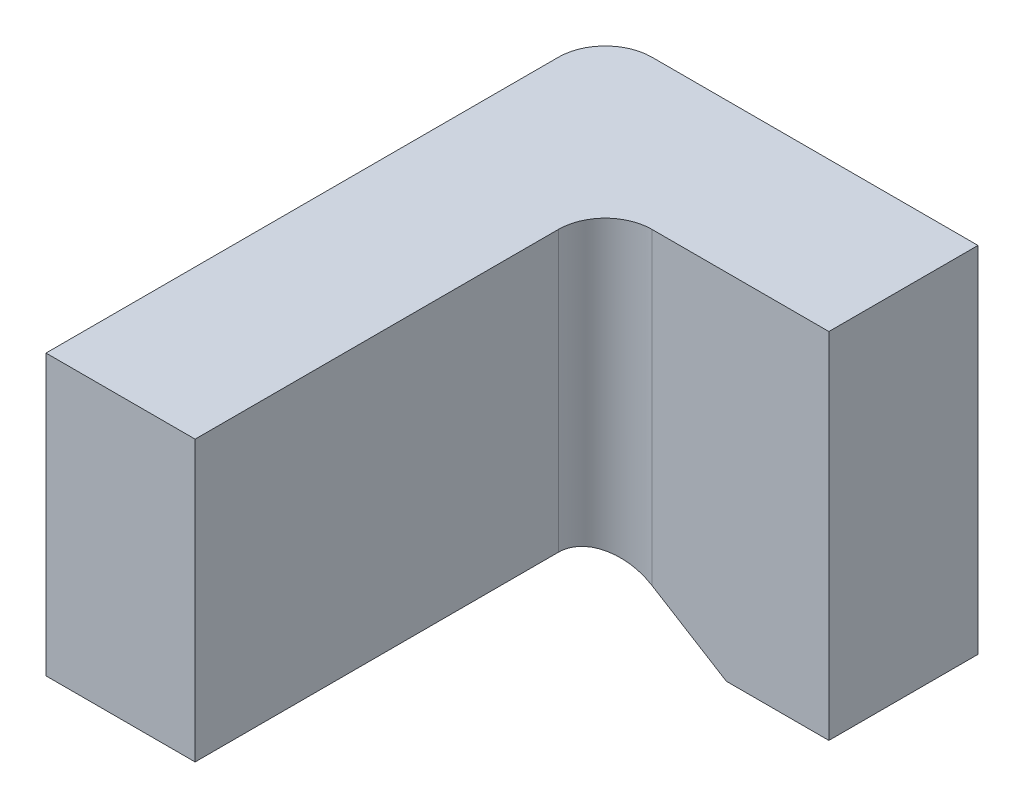
SolidWorks part; units mm, degrees
ref_plane "前视基准面" through (0, 0, 0) normal (0, 0, 1) x (1, 0, 0)
ref_plane "上视基准面" through (0, 0, 0) normal (0, 1, 0) x (1, 0, 0)
ref_plane "右视基准面" through (0, 0, 0) normal (1, 0, 0) x (0, 0, -1)
sketch "草图1" plane through (0, 0, 0) normal (0, 0, 1) x (1, 0, 0)
  line L0 (0, 0) -> (0.4, 0)
  line L1 (0.4, 0) -> (0.4, -0.38)
  line L2 (0.4, -0.38) -> (0.29, -0.38)
  line L3 (0.29, -0.38) -> (0.16, -0.3)
  line L4 (0.16, -0.3) -> (0, -0.3)
  line L5 (0, -0.3) -> (0, 0)
  dimension "D1" = 0.3
  dimension "D2" = 0.38
  dimension "D3" = 0.4
  dimension "D4" = 0.11
  dimension "D5" = 0.16
extrude "凸台-拉伸1" add sketch "草图1" along normal blind 0.16
sketch "草图2" plane through (0, 0, 0.16) normal (0, 0, 1) x (1, 0, 0)
  line L1 (0, 0) -> (0.16, 0)
  line L2 (0, 0) -> (0, -0.3)
  line L3 (0, -0.3) -> (0.16, -0.3)
  line L4 (0.16, 0) -> (0.16, -0.3)
extrude "凸台-拉伸2" add sketch "草图2" along normal blind 0.44
fillet "圆角1" radius 0.05 1 edges at (0, -0.15, 0)
fillet "圆角2" radius 0.05 1 edges at (0.16, -0.15, 0.16)
